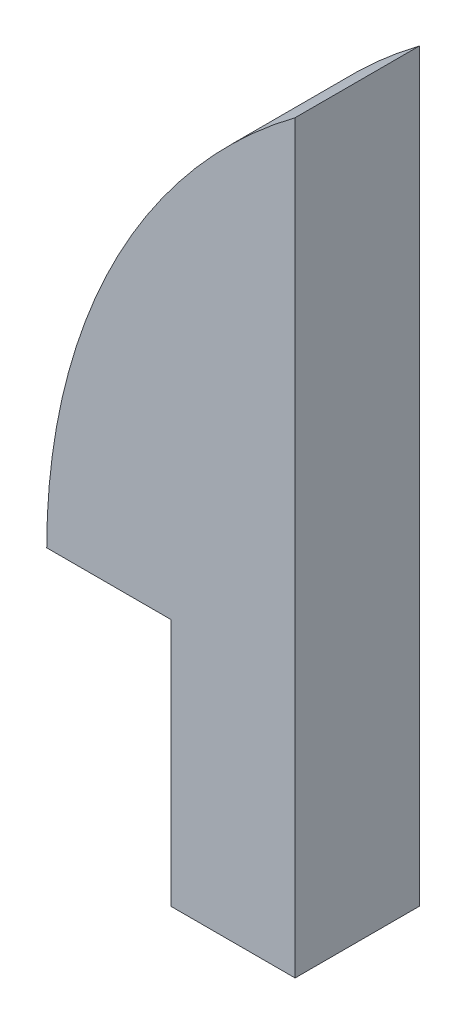
SolidWorks part; units mm, degrees
ref_plane "Front Plane" through (0, 0, 0) normal (0, 0, 1) x (1, 0, 0)
ref_plane "Top Plane" through (0, 0, 0) normal (0, 1, 0) x (1, 0, 0)
ref_plane "Right Plane" through (0, 0, 0) normal (1, 0, 0) x (0, 0, -1)
sketch "Sketch1" plane through (0, 0, 0) normal (0, 0, 1) x (1, 0, 0)
  line L1 (0, 0) -> (12.7, 0)
  line L2 (0, 0) -> (0, 38.1)
  line L3 (0, 38.1) -> (12.7, 38.1)
  line L4 (12.7, 0) -> (12.7, 38.1)
  line L5 (0, 12.7) -> (6.35, 12.7)
  line L6 (0, 12.7) -> (0, 0)
  line L7 (0, 0) -> (6.35, 0)
  line L8 (6.35, 12.7) -> (6.35, 0)
  arc A0 (0, 12.7) -> (12.7, 38.1) centre (31.75, 12.7) cw
  dimension "D1" = 6.35
  dimension "D2" = 12.7
  dimension "D3" = 12.7
  dimension "D4" = 38.1
extrude "Boss-Extrude1" add sketch "Sketch1" along normal blind 6.35 contours A0 L5 L8 L1 L4
